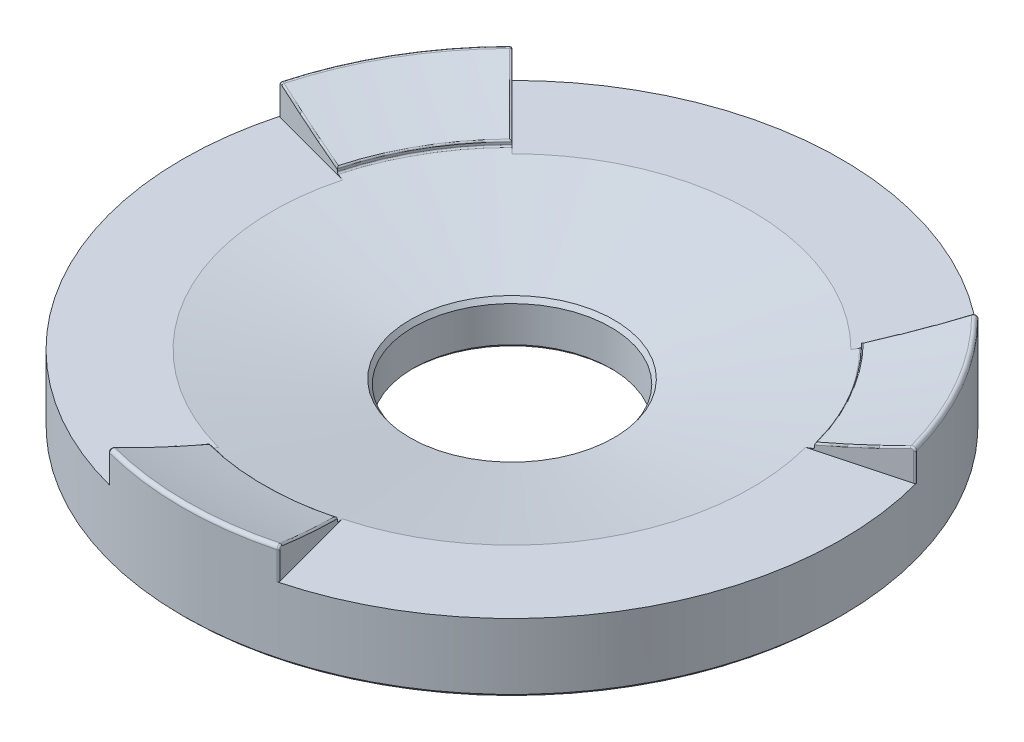
SolidWorks part; units mm, degrees
material "304 SSTL"
ref_plane "Front" through (0, 0, 0) normal (0, 0, 1) x (1, 0, 0)
ref_plane "Top" through (0, 0, 0) normal (0, 1, 0) x (1, 0, 0)
ref_plane "Right" through (0, 0, 0) normal (1, 0, 0) x (0, 0, -1)
sketch "Sketch1" plane through (0, 0, 0) normal (0, 0, 1) x (1, 0, 0)
  line L0 (0, 0) -> (0, -73.6473) construction
  line L2 (7.62, -76.9493) -> (25.4, -76.9493)
  line L3 (25.4, -76.9493) -> (25.4, -69.1286)
  line L6 (7.62, -73.252) -> (7.62, -76.9493)
  arc A0 (7.62, -73.252) -> (25.4, -69.1286) centre (0, 0) ccw construction
  arc A1 (7.62, -73.252) -> (25.4, -69.1286) centre (0, 0) ccw
  circle A2 centre (0, 0) radius 73.6473 construction
  dimension "D1" = 147.2946
  dimension "D2" = 7.62
  dimension "D3" = 25.4
  dimension "D4" = 3.302
revolve "Revolve1" add sketch "Sketch1" angle 360 about L0
sketch "Sketch4" plane through (0, 0, 0) normal (0, 0, 1) x (1, 0, 0)
  line L0 (7.62, -73.252) -> (7.62, -73.633)
  line L1 (7.62, -73.633) -> (19.05, -71.5219)
  line L2 (19.05, -71.5219) -> (19.05, -71.1409)
  line L3 (0, 0) -> (0, -85.9039) construction
  arc A0 (7.62, -73.252) -> (19.05, -71.1409) centre (0, 0) ccw
  dimension "D1" = 147.2946
  dimension "D2" = 0.381
  dimension "D3" = 0.381
  dimension "D4" = 7.62
  dimension "D5" = 11.43
revolve "Cut-Revolve2" cut sketch "Sketch4" angle 360 about L3
fillet "Fillet1" radius 0.254 1 edges at (-25.4, -69.1286, 0)
chamfer "Chamfer1" distance 0.254 angle 45 3 edges at (-7.62, -76.9493, 0) (0, -73.633, 7.62) (-25.4, -76.9493, 0)
sketch "Sketch5" plane through (0, 0, 0) normal (0, 1, 0) x (1, 0, 0)
  line L0 (0, 0) -> (0, 27.94) construction
  line L1 (-27.94, 27.94) -> (27.94, 27.94)
  line L2 (-27.94, 27.94) -> (0, 0)
  line L4 (27.94, 27.94) -> (0, 0)
  dimension "D1" = 90
  dimension "D2" = 27.94
extrude "Extrude1" cut sketch "Sketch5" against normal blind 71.628
pattern_circular "CirPattern1" count 3 over 360 about axis through (0, 0, 0) along (0, 1, 0) of "Extrude1"
fillet "Fillet4" radius 0.127 24 edges at (-24.5345, -70.5598, -6.574) (-24.4301, -69.2837, -6.546) (-17.9605, -70.5598, -17.9605) (-17.8841, -69.2837, -17.8841) (-6.574, -70.5598, 24.5345) (-6.546, -69.2837, 24.4301) (6.574, -70.5598, 24.5345) (6.546, -69.2837, 24.4301) (17.9605, -70.5598, -17.9605) (17.8841, -69.2837, -17.8841) (24.5345, -70.5598, -6.574) (24.4301, -69.2837, -6.546) (-21.3228, -70.2611, -5.7134) (-15.6094, -70.2611, -15.6094) (-16.4978, -71.1409, -9.525) (-16.4978, -71.5219, -9.525) (-5.7134, -70.2611, 21.3228) (0, -71.5219, 19.05) (0, -71.1409, 19.05) (5.7134, -70.2611, 21.3228) (16.4978, -71.5219, -9.525) (15.6094, -70.2611, -15.6094) (21.3228, -70.2611, -5.7134) (16.4978, -71.1409, -9.525)
